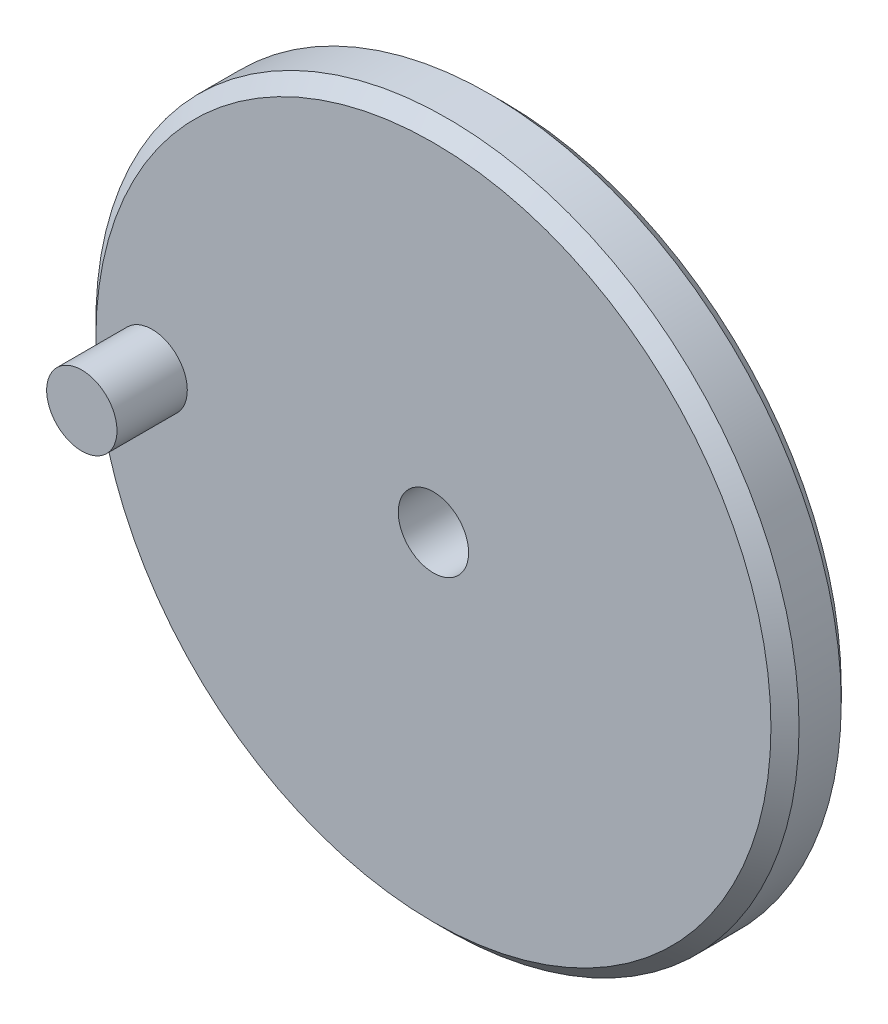
SolidWorks part; units mm, degrees
ref_plane "Front Plane" through (0, 0, 0) normal (0, 0, 1) x (1, 0, 0)
ref_plane "Top Plane" through (0, 0, 0) normal (0, 1, 0) x (1, 0, 0)
ref_plane "Right Plane" through (0, 0, 0) normal (1, 0, 0) x (0, 0, -1)
sketch "Sketch1" plane through (0, 0, 0) normal (0, 0, 1) x (1, 0, 0)
  circle A0 centre (0, 0) radius 25
  circle A1 centre (0, 0) radius 2.5
  dimension "D1" = 50
  dimension "D2" = 5
extrude "Boss-Extrude1" add sketch "Sketch1" along normal blind 5
sketch "Sketch2" plane through (0, 0, 5) normal (0, 0, 1) x (1, 0, 0)
  line L0 (0, 0) -> (-20, 0) construction
  circle A0 centre (-20, 0) radius 2.5
  dimension "D2" = 5
  dimension "D1" = 20
extrude "Boss-Extrude2" add sketch "Sketch2" along normal blind 5
chamfer "Chamfer1" distance 1 angle 45 2 edges at (25, 0, 5) (25, 0, 0)
